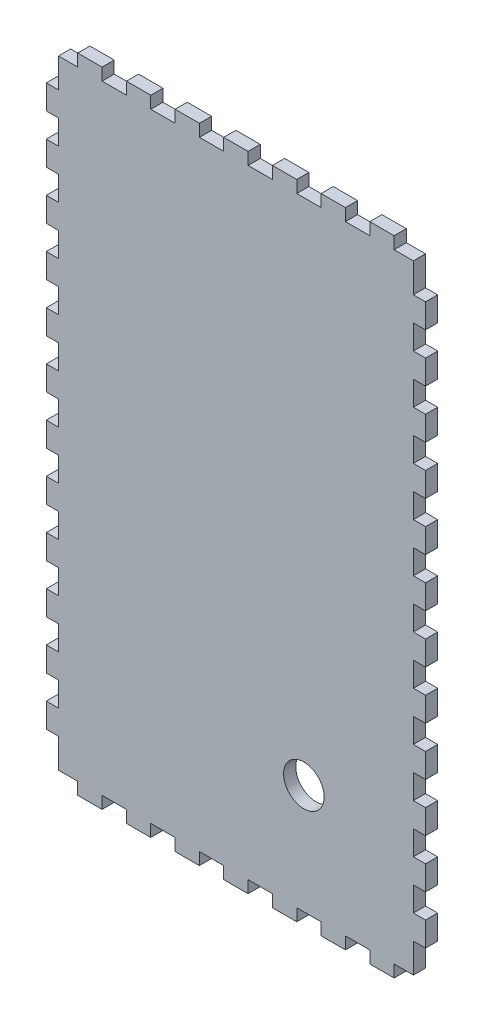
SolidWorks part; units mm, degrees
ref_plane "Front Plane" through (0, 0, 0) normal (0, 0, 1) x (1, 0, 0)
ref_plane "Top Plane" through (0, 0, 0) normal (0, 1, 0) x (1, 0, 0)
ref_plane "Right Plane" through (0, 0, 0) normal (1, 0, 0) x (0, 0, -1)
sketch "Sketch1" plane through (0, 0, 0) normal (0, 0, 1) x (1, 0, 0)
  line L0 (78, 0) -> (78, -6)
  line L1 (78, -6) -> (66, -6)
  line L2 (66, -6) -> (66, 0)
  line L3 (66, 0) -> (54, 0)
  line L4 (54, 0) -> (54, -6)
  line L5 (54, -6) -> (42, -6)
  line L6 (42, -6) -> (42, 0)
  line L7 (42, 0) -> (30, 0)
  line L8 (30, 0) -> (30, -6)
  line L9 (30, -6) -> (18, -6)
  line L10 (18, -6) -> (18, 0)
  line L11 (18, 0) -> (6, 0)
  line L12 (6, 0) -> (6, -6)
  line L13 (6, -6) -> (-6, -6)
  line L14 (-6, -6) -> (-6, 0)
  line L15 (-6, 0) -> (-18, 0)
  line L16 (-18, 0) -> (-18, -6)
  line L17 (-18, -6) -> (-30, -6)
  line L18 (-30, -6) -> (-30, 0)
  line L19 (-30, 0) -> (-42, 0)
  line L20 (-42, 0) -> (-42, -6)
  line L21 (-42, -6) -> (-54, -6)
  line L22 (-54, -6) -> (-54, 0)
  line L23 (-54, 0) -> (-66, 0)
  line L24 (-66, 0) -> (-66, -6)
  line L25 (-66, -6) -> (-78, -6)
  line L26 (-78, -6) -> (-78, 0)
  line L27 (-78, 0) -> (-87.5, 0)
  line L28 (-87.5, 0) -> (-87.5, 14.5)
  line L29 (-87.5, 14.5) -> (-93.5, 14.5)
  line L30 (-93.5, 14.5) -> (-93.5, 26.5)
  line L31 (-93.5, 26.5) -> (-87.5, 26.5)
  line L32 (-87.5, 26.5) -> (-87.5, 38.5)
  line L33 (-87.5, 38.5) -> (-93.5, 38.5)
  line L34 (-93.5, 38.5) -> (-93.5, 50.5)
  line L35 (-93.5, 38.5) -> (-93.5, 50.5) construction
  line L36 (-93.5, 50.5) -> (-87.5, 50.5)
  line L37 (-87.5, 62.5) -> (-93.5, 62.5)
  line L38 (-93.5, 62.5) -> (-93.5, 74.5)
  line L39 (-93.5, 74.5) -> (-87.5, 74.5)
  line L40 (-87.5, 74.5) -> (-87.5, 86.5)
  line L41 (-87.5, 86.5) -> (-93.5, 86.5)
  line L42 (-93.5, 86.5) -> (-93.5, 98.5)
  line L43 (-93.5, 98.5) -> (-87.5, 98.5)
  line L44 (-87.5, 98.5) -> (-87.5, 110.5)
  line L45 (-87.5, 110.5) -> (-93.5, 110.5)
  line L46 (-93.5, 110.5) -> (-93.5, 122.5)
  line L47 (-93.5, 122.5) -> (-87.5, 122.5)
  line L48 (-87.5, 122.5) -> (-87.5, 134.5)
  line L49 (-87.5, 134.5) -> (-93.5, 134.5)
  line L50 (-93.5, 134.5) -> (-93.5, 146.5)
  line L51 (-93.5, 146.5) -> (-87.5, 146.5)
  line L52 (-87.5, 146.5) -> (-87.5, 158.5)
  line L53 (-87.5, 158.5) -> (-93.5, 158.5)
  line L54 (-93.5, 158.5) -> (-93.5, 170.5)
  line L55 (-93.5, 170.5) -> (-87.5, 170.5)
  line L56 (-87.5, 158.5) -> (-87.5, 170.5) construction
  line L57 (-87.5, 170.5) -> (-87.5, 182.5)
  line L58 (-93.5, 182.5) -> (-87.5, 182.5) construction
  line L59 (-87.5, 182.5) -> (-93.5, 182.5)
  line L60 (-93.5, 182.5) -> (-93.5, 194.5)
  line L61 (-93.5, 194.5) -> (-87.5, 194.5)
  line L62 (-87.5, 194.5) -> (-87.5, 206.5)
  line L63 (-87.5, 206.5) -> (-93.5, 206.5)
  line L64 (-93.5, 206.5) -> (-93.5, 218.5)
  line L65 (-93.5, 218.5) -> (-87.5, 218.5)
  line L66 (-87.5, 218.5) -> (-87.5, 230.5)
  line L67 (-87.5, 230.5) -> (-93.5, 230.5)
  line L68 (-93.5, 230.5) -> (-93.5, 242.5)
  line L69 (-93.5, 242.5) -> (-87.5, 242.5)
  line L70 (-87.5, 242.5) -> (-87.5, 254.5)
  line L71 (-87.5, 254.5) -> (-87.5, 266.5) construction
  line L72 (-87.5, 254.5) -> (-93.5, 254.5)
  line L73 (-93.5, 254.5) -> (-87.5, 254.5) construction
  line L74 (-93.5, 254.5) -> (-93.5, 266.5)
  line L75 (-93.5, 266.5) -> (-87.5, 266.5)
  line L76 (-87.5, 266.5) -> (-87.5, 278.5)
  line L77 (-87.5, 278.5) -> (-93.5, 278.5)
  line L78 (-93.5, 278.5) -> (-93.5, 290.5)
  line L79 (-93.5, 290.5) -> (-87.5, 290.5)
  line L80 (-87.5, 290.5) -> (-87.5, 305)
  line L81 (-87.5, 305) -> (-78, 305)
  line L85 (-87.5, 50.5) -> (-87.5, 62.5)
  line L89 (87.5, 50.5) -> (87.5, 62.5)
  line L90 (87.5, 305) -> (78, 305)
  line L91 (87.5, 290.5) -> (87.5, 305)
  line L92 (93.5, 290.5) -> (87.5, 290.5)
  line L93 (93.5, 278.5) -> (93.5, 290.5)
  line L94 (87.5, 278.5) -> (93.5, 278.5)
  line L95 (87.5, 266.5) -> (87.5, 278.5)
  line L96 (93.5, 266.5) -> (87.5, 266.5)
  line L97 (93.5, 254.5) -> (93.5, 266.5)
  line L98 (87.5, 254.5) -> (93.5, 254.5)
  line L99 (87.5, 242.5) -> (87.5, 254.5)
  line L100 (93.5, 242.5) -> (87.5, 242.5)
  line L101 (93.5, 230.5) -> (93.5, 242.5)
  line L102 (87.5, 230.5) -> (93.5, 230.5)
  line L103 (87.5, 218.5) -> (87.5, 230.5)
  line L104 (93.5, 218.5) -> (87.5, 218.5)
  line L105 (93.5, 206.5) -> (93.5, 218.5)
  line L106 (87.5, 206.5) -> (93.5, 206.5)
  line L107 (87.5, 194.5) -> (87.5, 206.5)
  line L108 (93.5, 194.5) -> (87.5, 194.5)
  line L109 (93.5, 182.5) -> (93.5, 194.5)
  line L110 (87.5, 182.5) -> (93.5, 182.5)
  line L111 (87.5, 170.5) -> (87.5, 182.5)
  line L112 (93.5, 170.5) -> (87.5, 170.5)
  line L113 (93.5, 158.5) -> (93.5, 170.5)
  line L114 (87.5, 158.5) -> (93.5, 158.5)
  line L115 (87.5, 146.5) -> (87.5, 158.5)
  line L116 (93.5, 146.5) -> (87.5, 146.5)
  line L117 (93.5, 134.5) -> (93.5, 146.5)
  line L118 (87.5, 134.5) -> (93.5, 134.5)
  line L119 (87.5, 122.5) -> (87.5, 134.5)
  line L120 (93.5, 122.5) -> (87.5, 122.5)
  line L121 (93.5, 110.5) -> (93.5, 122.5)
  line L122 (87.5, 110.5) -> (93.5, 110.5)
  line L123 (87.5, 98.5) -> (87.5, 110.5)
  line L124 (93.5, 98.5) -> (87.5, 98.5)
  line L125 (93.5, 86.5) -> (93.5, 98.5)
  line L126 (87.5, 86.5) -> (93.5, 86.5)
  line L127 (87.5, 74.5) -> (87.5, 86.5)
  line L128 (93.5, 74.5) -> (87.5, 74.5)
  line L129 (93.5, 62.5) -> (93.5, 74.5)
  line L130 (87.5, 62.5) -> (93.5, 62.5)
  line L131 (93.5, 50.5) -> (87.5, 50.5)
  line L132 (93.5, 38.5) -> (93.5, 50.5)
  line L133 (87.5, 38.5) -> (93.5, 38.5)
  line L134 (87.5, 26.5) -> (87.5, 38.5)
  line L135 (93.5, 26.5) -> (87.5, 26.5)
  line L136 (93.5, 14.5) -> (93.5, 26.5)
  line L137 (87.5, 14.5) -> (93.5, 14.5)
  line L138 (87.5, 0) -> (87.5, 14.5)
  line L139 (78, 0) -> (87.5, 0)
  line L140 (-78, 311) -> (-78, 305)
  line L141 (-66, 311) -> (-78, 311)
  line L142 (-66, 305) -> (-66, 311)
  line L143 (-54, 305) -> (-66, 305)
  line L144 (-54, 311) -> (-54, 305)
  line L145 (-42, 311) -> (-54, 311)
  line L146 (-42, 305) -> (-42, 311)
  line L147 (-30, 305) -> (-42, 305)
  line L148 (-30, 311) -> (-30, 305)
  line L149 (-18, 311) -> (-30, 311)
  line L150 (-18, 305) -> (-18, 311)
  line L151 (-6, 305) -> (-18, 305)
  line L152 (-6, 311) -> (-6, 305)
  line L153 (6, 311) -> (-6, 311)
  line L154 (6, 305) -> (6, 311)
  line L155 (18, 305) -> (6, 305)
  line L156 (18, 311) -> (18, 305)
  line L157 (30, 311) -> (18, 311)
  line L158 (30, 305) -> (30, 311)
  line L159 (42, 305) -> (30, 305)
  line L160 (42, 311) -> (42, 305)
  line L161 (54, 311) -> (42, 311)
  line L162 (54, 305) -> (54, 311)
  line L163 (66, 305) -> (54, 305)
  line L164 (66, 311) -> (66, 305)
  line L165 (78, 311) -> (66, 311)
  line L166 (78, 305) -> (78, 311)
  circle A0 centre (33.5, 54) radius 10
  point P156 (0, 152.5)
  dimension "D1" = 20
  dimension "D2" = 60
  dimension "D3" = 60
extrude "Boss-Extrude1" add sketch "Sketch1" along normal blind 6
